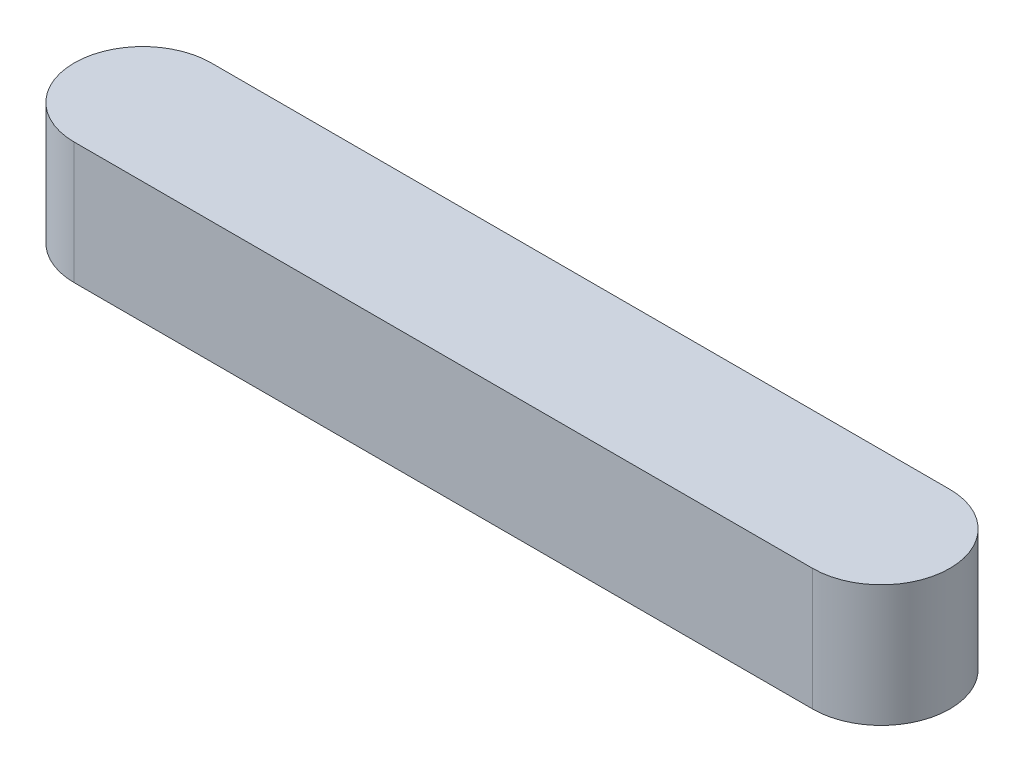
SolidWorks part; units mm, degrees
ref_plane "Front Plane" through (0, 0, 0) normal (0, 0, 1) x (1, 0, 0)
ref_plane "Top Plane" through (0, 0, 0) normal (0, 1, 0) x (1, 0, 0)
ref_plane "Right Plane" through (0, 0, 0) normal (1, 0, 0) x (0, 0, -1)
sketch "Sketch1" plane through (0, 0, 0) normal (0, 1, 0) x (1, 0, 0)
  line L0 (-57.5, 0) -> (57.5, 0) construction
  line L1 (-48.5, 0) -> (48.5, 0) construction
  line L2 (-48.5, 9) -> (48.5, 9)
  line L3 (-48.5, -9) -> (48.5, -9)
  arc A0 (-48.5, 9) -> (-48.5, -9) centre (-48.5, 0) ccw
  arc A1 (48.5, -9) -> (48.5, 9) centre (48.5, 0) ccw
  point P4 (0, 0)
  point P7 (0, 0)
  point P12 (0, 0)
  point P13 (0, 0)
  point P14 (0, 0)
  point P15 (0, 0)
  dimension "D" = 9
  dimension "L" = 115
extrude "Boss-Extrude1" add sketch "Sketch1" along normal blind 16
sketch "Sketch2" plane through (0, 16, 0) normal (0, 1, 0) x (1, 0, 0)
  line L0 (48.5, 9) -> (-48.5, 9) construction
  line L1 (0, 9) -> (57.5, 9)
  line L2 (0, 9) -> (0, -9)
  line L3 (0, -9) -> (57.5, -9)
  line L4 (57.5, 9) -> (57.5, -9)
  line L5 (-48.5, -9) -> (48.5, -9) construction
  arc A0 (48.5, -9) -> (48.5, 9) centre (48.5, 0) ccw construction
  point P6 (0, 0)
extrude "Cut-Extrude1" [suppressed] cut sketch "Sketch2" against normal through all
equation "\"L\" = 115"
equation "\"D\" = 9"
equation "\"H\"= 16"
equation "\"Cut-Extrude1\"= IIF ( \"L\" = 160 , \"unsuppressed\" , IIF ( \"L\" = 100 , \"unsuppressed\" , \"suppressed\" ) )"
equation "\"L@Sketch1\"=\"L\""
equation "\"D@Sketch1\"=\"D\""
equation "\"H@Boss-Extrude1\"=\"H\""
